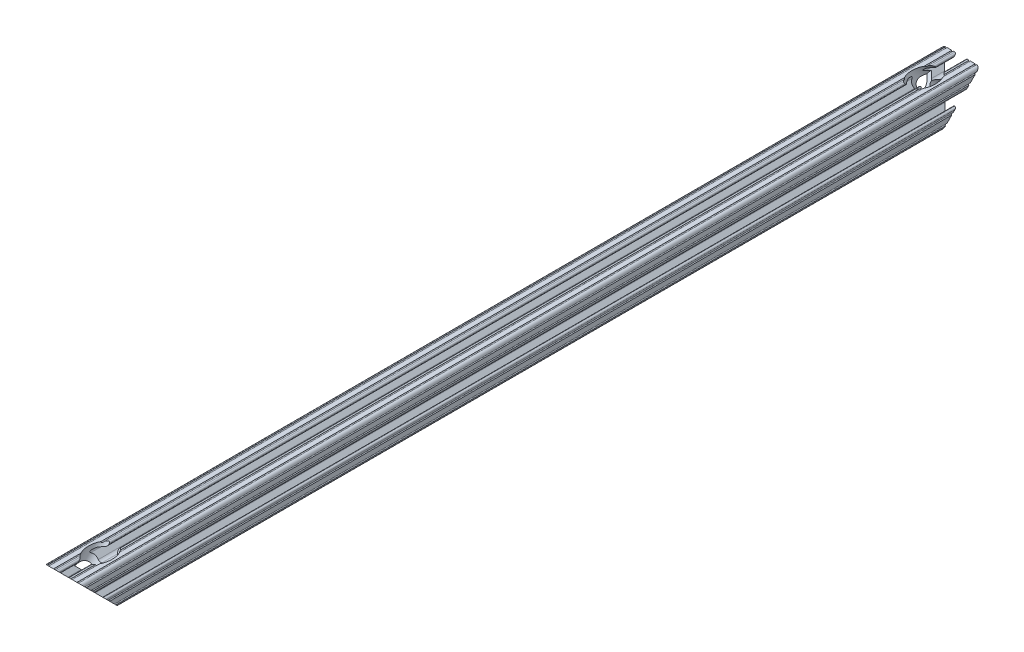
SolidWorks part; units mm, degrees
ref_plane "Front Plane" through (0, 0, 0) normal (0, 0, 1) x (1, 0, 0)
ref_plane "Top Plane" through (0, 0, 0) normal (0, 1, 0) x (1, 0, 0)
ref_plane "Right Plane" through (0, 0, 0) normal (1, 0, 0) x (0, 0, -1)
sketch "Sketch1" plane through (0, 0, 0) normal (0, 0, 1) x (1, 0, 0)
  line L2 (-7.1797, -8.6452) -> (-3.9523, -5.4237)
  line L3 (-1.7093, -4.4958) -> (1.7093, -4.4958)
  line L4 (3.9523, -5.4237) -> (7.1797, -8.6452)
  line L6 (6.4164, -10.4902) -> (4.2875, -10.4902)
  line L7 (3.2385, -11.5392) -> (3.2385, -11.651)
  line L8 (4.2875, -12.7) -> (5.3171, -12.7)
  line L9 (6.3331, -12.7) -> (9.5504, -12.7)
  line L10 (12.7, -9.5504) -> (12.7, -6.3331)
  line L11 (12.7, -5.3171) -> (12.7, -4.2875)
  line L12 (11.651, -3.2385) -> (11.5392, -3.2385)
  line L13 (10.4902, -4.2875) -> (10.4902, -6.4021)
  line L14 (8.7371, -7.1294) -> (5.441, -3.8408)
  line L15 (4.5085, -1.5932) -> (4.5085, 1.5932)
  line L16 (5.441, 3.8408) -> (8.7371, 7.1294)
  line L17 (10.4902, 6.4021) -> (10.4902, 4.2875)
  line L18 (11.5392, 3.2385) -> (11.651, 3.2385)
  line L19 (12.7, 4.2875) -> (12.7, 5.3171)
  line L20 (12.7, 6.3331) -> (12.7, 9.5504)
  line L21 (9.5504, 12.7) -> (6.3331, 12.7)
  line L22 (5.3171, 12.7) -> (4.2875, 12.7)
  line L23 (3.2385, 11.651) -> (3.2385, 11.5392)
  line L24 (4.2875, 10.4902) -> (6.4768, 10.4902)
  line L25 (7.207, 8.7244) -> (3.8983, 5.4232)
  line L26 (1.6558, 4.4958) -> (-1.6558, 4.4958)
  line L27 (-3.8983, 5.4232) -> (-7.207, 8.7244)
  line L28 (-6.4768, 10.4902) -> (-4.2875, 10.4902)
  line L29 (-3.2385, 11.5392) -> (-3.2385, 11.651)
  line L30 (-4.2875, 12.7) -> (-5.3171, 12.7)
  line L31 (-6.3331, 12.7) -> (-9.5504, 12.7)
  line L32 (-12.7, 9.5504) -> (-12.7, 6.3331)
  line L33 (-12.7, 5.3171) -> (-12.7, 4.2875)
  line L34 (-11.651, 3.2385) -> (-11.5392, 3.2385)
  line L35 (-10.4902, 4.2875) -> (-10.4902, 6.4021)
  line L36 (-8.7371, 7.1294) -> (-5.441, 3.8408)
  line L37 (-4.5085, 1.5932) -> (-4.5085, -1.5932)
  line L38 (-5.441, -3.8408) -> (-8.7371, -7.1294)
  line L39 (-10.4902, -6.4021) -> (-10.4902, -4.2875)
  line L40 (-11.5392, -3.2385) -> (-11.651, -3.2385)
  line L41 (-12.7, -4.2875) -> (-12.7, -5.3171)
  line L42 (-12.7, -6.3331) -> (-12.7, -9.5504)
  line L43 (-9.5504, -12.7) -> (-6.3331, -12.7)
  line L44 (-5.3171, -12.7) -> (-4.2875, -12.7)
  line L45 (-3.2385, -11.651) -> (-3.2385, -11.5392)
  line L46 (-4.2875, -10.4902) -> (-6.4164, -10.4902)
  circle A0 centre (0, 0) radius 2.6035
  arc A1 (-7.1797, -8.6452) -> (-6.4164, -10.4902) centre (-6.4164, -9.4098) ccw
  arc A2 (-1.7093, -4.4958) -> (-3.9523, -5.4237) centre (-1.7093, -7.6708) ccw
  arc A3 (3.9523, -5.4237) -> (1.7093, -4.4958) centre (1.7093, -7.6708) ccw
  arc A4 (6.4164, -10.4902) -> (7.1797, -8.6452) centre (6.4164, -9.4098) ccw
  arc A5 (4.2875, -10.4902) -> (3.2385, -11.5392) centre (4.2875, -11.5392) ccw
  arc A6 (3.2385, -11.651) -> (4.2875, -12.7) centre (4.2875, -11.651) ccw
  arc A7 (6.3331, -12.7) -> (5.3171, -12.7) centre (5.8251, -12.7) ccw
  arc A8 (10.5664, -12.6998) -> (9.5504, -12.7) centre (10.0584, -12.7) ccw
  arc A9 (10.5664, -12.6998) -> (12.6998, -10.5664) centre (10.5918, -10.5918) ccw
  arc A10 (12.7, -9.5504) -> (12.6998, -10.5664) centre (12.7, -10.0584) ccw
  arc A11 (12.7, -5.3171) -> (12.7, -6.3331) centre (12.7, -5.8251) ccw
  arc A12 (12.7, -4.2875) -> (11.651, -3.2385) centre (11.651, -4.2875) ccw
  arc A13 (11.5392, -3.2385) -> (10.4902, -4.2875) centre (11.5392, -4.2875) ccw
  arc A14 (8.7371, -7.1294) -> (10.4902, -6.4021) centre (9.4628, -6.4021) ccw
  arc A15 (4.5085, -1.5932) -> (5.441, -3.8408) centre (7.6835, -1.5932) ccw
  arc A16 (5.441, 3.8408) -> (4.5085, 1.5932) centre (7.6835, 1.5932) ccw
  arc A17 (10.4902, 6.4021) -> (8.7371, 7.1294) centre (9.4628, 6.4021) ccw
  arc A18 (10.4902, 4.2875) -> (11.5392, 3.2385) centre (11.5392, 4.2875) ccw
  arc A19 (11.651, 3.2385) -> (12.7, 4.2875) centre (11.651, 4.2875) ccw
  arc A20 (12.7, 6.3331) -> (12.7, 5.3171) centre (12.7, 5.8251) ccw
  arc A21 (12.6998, 10.5664) -> (12.7, 9.5504) centre (12.7, 10.0584) ccw
  arc A22 (12.6998, 10.5664) -> (10.5664, 12.6998) centre (10.5918, 10.5918) ccw
  arc A23 (9.5504, 12.7) -> (10.5664, 12.6998) centre (10.0584, 12.7) ccw
  arc A24 (5.3171, 12.7) -> (6.3331, 12.7) centre (5.8251, 12.7) ccw
  arc A25 (4.2875, 12.7) -> (3.2385, 11.651) centre (4.2875, 11.651) ccw
  arc A26 (3.2385, 11.5392) -> (4.2875, 10.4902) centre (4.2875, 11.5392) ccw
  arc A27 (7.207, 8.7244) -> (6.4768, 10.4902) centre (6.4768, 9.4563) ccw
  arc A28 (1.6558, 4.4958) -> (3.8983, 5.4232) centre (1.6558, 7.6708) ccw
  arc A29 (-3.8983, 5.4232) -> (-1.6558, 4.4958) centre (-1.6558, 7.6708) ccw
  arc A30 (-6.4768, 10.4902) -> (-7.207, 8.7244) centre (-6.4768, 9.4563) ccw
  arc A31 (-4.2875, 10.4902) -> (-3.2385, 11.5392) centre (-4.2875, 11.5392) ccw
  arc A32 (-3.2385, 11.651) -> (-4.2875, 12.7) centre (-4.2875, 11.651) ccw
  arc A33 (-6.3331, 12.7) -> (-5.3171, 12.7) centre (-5.8251, 12.7) ccw
  arc A34 (-10.5664, 12.6998) -> (-9.5504, 12.7) centre (-10.0584, 12.7) ccw
  arc A35 (-10.5664, 12.6998) -> (-12.6998, 10.5664) centre (-10.5918, 10.5918) ccw
  arc A36 (-12.7, 9.5504) -> (-12.6998, 10.5664) centre (-12.7, 10.0584) ccw
  arc A37 (-12.7, 5.3171) -> (-12.7, 6.3331) centre (-12.7, 5.8251) ccw
  arc A38 (-12.7, 4.2875) -> (-11.651, 3.2385) centre (-11.651, 4.2875) ccw
  arc A39 (-11.5392, 3.2385) -> (-10.4902, 4.2875) centre (-11.5392, 4.2875) ccw
  arc A40 (-8.7371, 7.1294) -> (-10.4902, 6.4021) centre (-9.4628, 6.4021) ccw
  arc A41 (-4.5085, 1.5932) -> (-5.441, 3.8408) centre (-7.6835, 1.5932) ccw
  arc A42 (-5.441, -3.8408) -> (-4.5085, -1.5932) centre (-7.6835, -1.5932) ccw
  arc A43 (-10.4902, -6.4021) -> (-8.7371, -7.1294) centre (-9.4628, -6.4021) ccw
  arc A44 (-10.4902, -4.2875) -> (-11.5392, -3.2385) centre (-11.5392, -4.2875) ccw
  arc A45 (-11.651, -3.2385) -> (-12.7, -4.2875) centre (-11.651, -4.2875) ccw
  arc A46 (-12.7, -6.3331) -> (-12.7, -5.3171) centre (-12.7, -5.8251) ccw
  arc A47 (-12.6998, -10.5664) -> (-12.7, -9.5504) centre (-12.7, -10.0584) ccw
  arc A48 (-12.6998, -10.5664) -> (-10.5664, -12.6998) centre (-10.5918, -10.5918) ccw
  arc A49 (-9.5504, -12.7) -> (-10.5664, -12.6998) centre (-10.0584, -12.7) ccw
  arc A50 (-5.3171, -12.7) -> (-6.3331, -12.7) centre (-5.8251, -12.7) ccw
  arc A51 (-4.2875, -12.7) -> (-3.2385, -11.651) centre (-4.2875, -11.651) ccw
  arc A52 (-3.2385, -11.5392) -> (-4.2875, -10.4902) centre (-4.2875, -11.5392) ccw
extrude "Boss-Extrude1" add sketch "Sketch1" along normal mid plane 609.6
sketch "Sketch2" plane through (0, 0, 0) normal (1, 0, 0) x (0, 0, -1)
  line L0 (-304.8, 12.6998) -> (-304.8, -12.7)
  line L1 (-304.8, -12.7) -> (-279.4002, -12.7)
  line L2 (-279.4002, -12.7) -> (-304.8, 12.6998)
  line L3 (0, 0) -> (0, -12.7) construction
  line L5 (279.4002, -12.7) -> (304.8, 12.6998)
  line L6 (304.8, -12.7) -> (279.4002, -12.7)
  line L7 (304.8, 12.6998) -> (304.8, -12.7)
  line L8 (-304.8, -12.7) -> (304.8, -12.7) construction
extrude "Cut-Extrude1" cut sketch "Sketch2" against normal through all and the other way through all
sketch "Sketch3" plane through (0, 0, 0) normal (1, 0, 0) x (0, 0, -1)
  line L0 (-273.7876, 18.3125) -> (-292.1002, 0)
  line L1 (-292.1002, 0) -> (-294.4081, 2.3079)
  line L2 (-294.4081, 2.3079) -> (-289.918, 6.7981)
  line L3 (-289.918, 6.7981) -> (-293.2227, 10.1028)
  line L4 (-293.2227, 10.1028) -> (-279.4003, 23.9252)
  line L5 (-279.4003, 23.9252) -> (-273.7876, 18.3125)
  line L6 (-292.1002, 0) -> (-294.4081, -2.3079) construction
  line L7 (-279.4002, -12.7) -> (-304.8, 12.6998) construction
  line L8 (-294.7037, 2.6035) -> (-289.4967, -2.6035) construction
  line L9 (-281.9974, -1.1225) -> (-268.175, 12.6998) construction
  dimension "D1" = 6.5278
  dimension "D2" = 15.875
  dimension "D3" = 6.35
revolve "Cut-Revolve1" cut sketch "Sketch3" angle 360 about L6
mirror "Mirror1" about plane through (0, 0, 0) normal (0, 0, 1) of "Cut-Revolve1"
